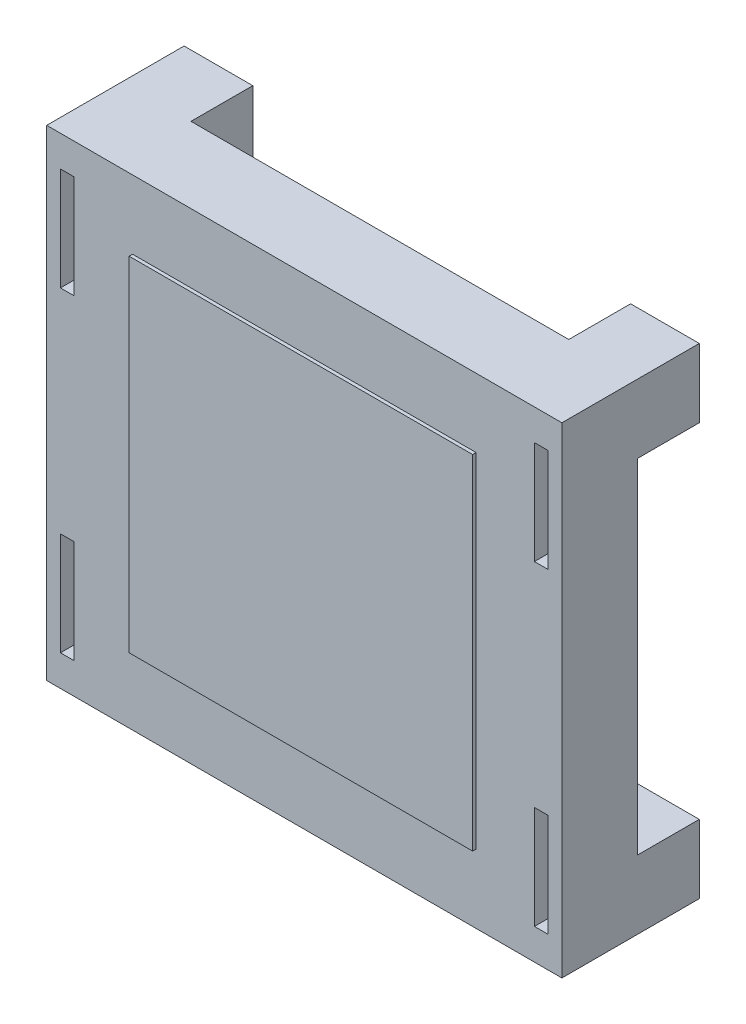
SolidWorks part; units mm, degrees
ref_plane "Front Plane" through (0, 0, 0) normal (0, 0, 1) x (1, 0, 0)
ref_plane "Top Plane" through (0, 0, 0) normal (0, 1, 0) x (1, 0, 0)
ref_plane "Right Plane" through (0, 0, 0) normal (1, 0, 0) x (0, 0, -1)
sketch "Sketch1" plane through (0, 0, 0) normal (0, 0, 1) x (1, 0, 0)
  line L1 (-187.5, -175) -> (187.5, -175)
  line L2 (-187.5, -175) -> (-187.5, 175)
  line L3 (-187.5, 175) -> (187.5, 175)
  line L4 (187.5, -175) -> (187.5, 175)
  line L5 (-187.5, -175) -> (187.5, 175) construction
  line L6 (-187.5, 175) -> (187.5, -175) construction
  point P0 (0, 0)
  dimension "D1" = 375
  dimension "D2" = 350
extrude "Boss-Extrude1" add sketch "Sketch1" along normal blind 100
sketch "Sketch2" plane through (0, 175, 0) normal (0, 1, 0) x (1, 0, 0)
  line L0 (187.5, 0) -> (-187.5, 0) construction
  line L1 (-137.5, 0) -> (137.5, 0)
  line L2 (-137.5, 0) -> (-137.5, -45)
  line L3 (-137.5, -45) -> (137.5, -45)
  line L4 (137.5, 0) -> (137.5, -45)
  line L5 (187.5, -100) -> (187.5, 0) construction
  line L6 (-187.5, -100) -> (-187.5, 0) construction
  dimension "D1" = 50
  dimension "D2" = 50
  dimension "D3" = 45
extrude "Cut-Extrude1" cut sketch "Sketch2" against normal through all
sketch "Sketch3" plane through (-187.5, 0, 0) normal (-1, 0, 0) x (0, 0, 1)
  line L0 (0, 175) -> (0, -175) construction
  line L1 (0, 125) -> (45, 125)
  line L2 (0, 125) -> (0, -125)
  line L3 (0, -125) -> (45, -125)
  line L4 (45, 125) -> (45, -125)
  line L5 (100, 175) -> (0, 175) construction
  line L6 (100, -175) -> (0, -175) construction
  dimension "D1" = 50
  dimension "D2" = 50
  dimension "D3" = 45
extrude "Cut-Extrude2" cut sketch "Sketch3" against normal through all
sketch "Sketch4" plane through (0, 0, 100) normal (0, 0, 1) x (1, 0, 0)
  line L1 (-125, -125) -> (125, -125)
  line L2 (-125, -125) -> (-125, 125)
  line L3 (-125, 125) -> (125, 125)
  line L4 (125, -125) -> (125, 125)
  line L5 (-125, -125) -> (125, 125) construction
  line L6 (-125, 125) -> (125, -125) construction
  point P0 (0, 0)
  dimension "D1" = 250
  dimension "D2" = 250
extrude "Boss-Extrude2" add sketch "Sketch4" along normal blind 2.5
sketch "Sketch5" plane through (0, 0, 100) normal (0, 0, 1) x (1, 0, 0)
  line L0 (0, 175) -> (0, -175) construction
  line L1 (187.5, 175) -> (-187.5, 175) construction
  line L2 (-187.5, -175) -> (187.5, -175) construction
  line L3 (-187.5, 0) -> (187.5, 0) construction
  line L4 (-187.5, 175) -> (-187.5, -175) construction
  line L5 (187.5, -175) -> (187.5, 175) construction
  line L6 (187.5, 115) -> (130.5, 115) construction
  line L7 (187.5, 175) -> (130.5, 175)
  line L8 (187.5, 175) -> (187.5, 55)
  line L9 (187.5, 55) -> (130.5, 55)
  line L10 (130.5, 175) -> (130.5, 55)
  line L11 (-167.5, 152.5) -> (-177.5, 152.5)
  line L12 (167.5, 77.5) -> (177.5, 77.5)
  line L13 (167.5, 77.5) -> (167.5, 152.5)
  line L14 (167.5, 152.5) -> (177.5, 152.5)
  line L15 (177.5, 77.5) -> (177.5, 152.5)
  line L16 (167.5, 77.5) -> (177.5, 152.5) construction
  line L17 (167.5, 152.5) -> (177.5, 77.5) construction
  line L18 (-177.5, 77.5) -> (-177.5, 152.5)
  line L19 (-167.5, 77.5) -> (-177.5, 77.5)
  line L20 (-167.5, 77.5) -> (-167.5, 152.5)
  line L21 (167.5, -152.5) -> (177.5, -152.5)
  line L22 (177.5, -77.5) -> (177.5, -152.5)
  line L23 (167.5, -77.5) -> (177.5, -77.5)
  line L24 (167.5, -77.5) -> (167.5, -152.5)
  line L25 (-167.5, -77.5) -> (-167.5, -152.5)
  line L26 (-167.5, -77.5) -> (-177.5, -77.5)
  line L27 (-177.5, -77.5) -> (-177.5, -152.5)
  line L28 (-167.5, -152.5) -> (-177.5, -152.5)
  point P19 (172.5, 115)
  dimension "D1" = 57
  dimension "D2" = 120
  dimension "D3" = 10
  dimension "D4" = 75
  dimension "D5" = 10
extrude "Cut-Extrude4" cut sketch "Sketch5" against normal blind 50 contours L19 L20 L11 L18 | L28 L25 L26 L27 | L23 L24 L21 L22 | L12 L15 L14 L13
sketch "Sketch6" plane through (0, -175, 0) normal (0, -1, 0) x (1, 0, 0)
  line L0 (-187.5, 72.5) -> (187.5, 72.5) construction
  line L1 (-187.5, 100) -> (-187.5, 0) construction
  line L2 (187.5, 100) -> (187.5, 0) construction
  line L3 (-187.5, 100) -> (187.5, 100) construction
  text T0 "CBU ROBOTICS CLUB" font "Century Gothic" height 15
  dimension "D1" = 27.5
extrude "Boss-Extrude3" add sketch "Sketch6" along normal blind 2.5
